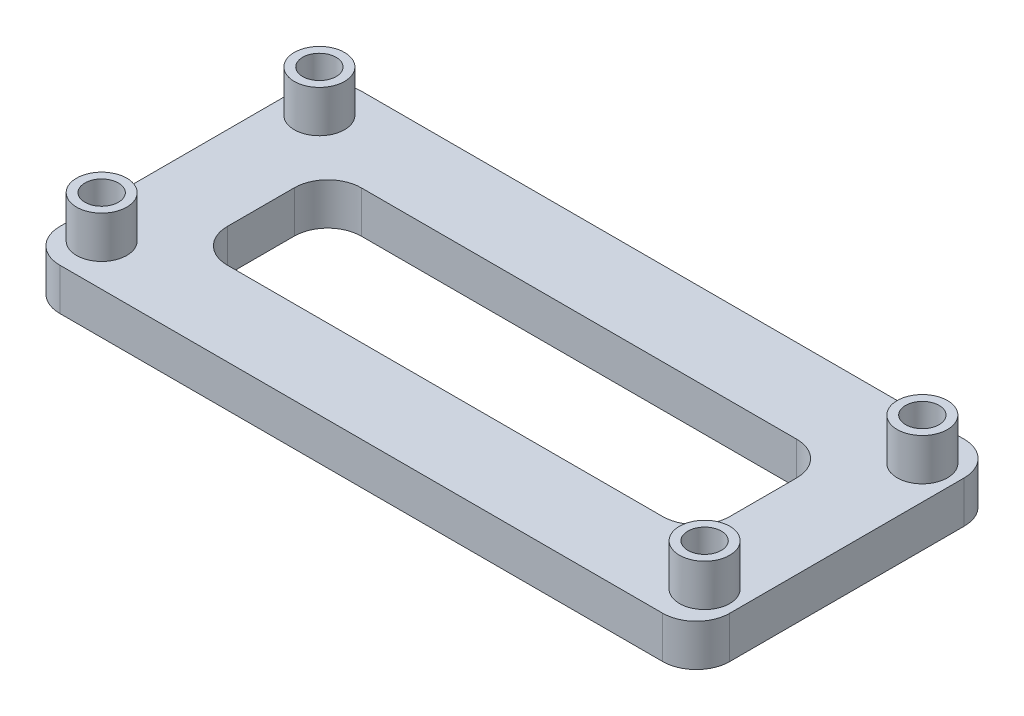
SolidWorks part; units mm, degrees
ref_plane "Front Plane" through (0, 0, 0) normal (0, 0, 1) x (1, 0, 0)
ref_plane "Top Plane" through (0, 0, 0) normal (0, 1, 0) x (1, 0, 0)
ref_plane "Right Plane" through (0, 0, 0) normal (1, 0, 0) x (0, 0, -1)
sketch "Sketch1" plane through (0, 0, 0) normal (0, 1, 0) x (1, 0, 0)
  line L1 (0, 0) -> (50.8, 0)
  line L2 (0, 0) -> (0, 22.86)
  line L3 (0, 22.86) -> (50.8, 22.86)
  line L4 (50.8, 0) -> (50.8, 22.86)
  line L5 (6.35, 16.51) -> (44.45, 16.51)
  line L6 (6.35, 16.51) -> (6.35, 6.35)
  line L7 (6.35, 6.35) -> (44.45, 6.35)
  line L8 (44.45, 16.51) -> (44.45, 6.35)
  circle A0 centre (2.54, 19.685) radius 1.27
  circle A1 centre (48.26, 19.685) radius 1.27
  circle A2 centre (2.54, 3.175) radius 1.27
  circle A3 centre (48.26, 3.175) radius 1.27
  dimension "D3" = 2.54
  dimension "D4" = 2.54
  dimension "D5" = 2.54
  dimension "D6" = 2.54
  dimension "D1" = 22.86
  dimension "D2" = 50.8
  dimension "D7" = 45.72
  dimension "D8" = 16.51
  dimension "D9" = 3.175
  dimension "D10" = 2.54
  dimension "D11" = 6.35
  dimension "D12" = 38.1
  dimension "D13" = 6.35
  dimension "D14" = 10.16
extrude "Boss-Extrude1" add sketch "Sketch1" along normal blind 3.175
sketch "Sketch2" plane through (0, 3.175, 0) normal (0, 1, 0) x (1, 0, 0)
  line L0 (0, 11.43) -> (50.8, 11.43) construction
  line L1 (0, 22.86) -> (0, 0) construction
  line L2 (50.8, 0) -> (50.8, 22.86) construction
  line L3 (25.4, 22.86) -> (25.4, 0) construction
  line L4 (50.8, 22.86) -> (0, 22.86) construction
  line L5 (0, 0) -> (50.8, 0) construction
  circle A0 centre (2.54, 19.685) radius 1.905
  circle A1 centre (2.54, 19.685) radius 1.27
  circle A2 centre (2.54, 3.175) radius 1.27
  circle A3 centre (2.54, 3.175) radius 1.905
  circle A4 centre (48.26, 3.175) radius 1.27
  circle A5 centre (48.26, 3.175) radius 1.905
  circle A6 centre (48.26, 19.685) radius 1.27
  circle A7 centre (48.26, 19.685) radius 1.905
  dimension "D1" = 3.81
  dimension "D2" = 2.54
extrude "Boss-Extrude2" add sketch "Sketch2" along normal blind 3.175
fillet "Fillet1" radius 2.54 8 edges at (50.8, 1.5875, 0) (50.8, 1.5875, -22.86) (0, 1.5875, -22.86) (0, 1.5875, 0) (6.35, 1.5875, -6.35) (44.45, 1.5875, -6.35) (44.45, 1.5875, -16.51) (6.35, 1.5875, -16.51)
equation "\"D4@Sketch1\"=\"D3@Sketch1\""
equation "\"D5@Sketch1\"=\"D3@Sketch1\""
equation "\"D6@Sketch1\"=\"D3@Sketch1\""
equation "\"D9@Sketch1\"=(\"D1@Sketch1\"-\"D8@Sketch1\")/2"
equation "\"D10@Sketch1\"=(\"D2@Sketch1\"-\"D7@Sketch1\")/2"
